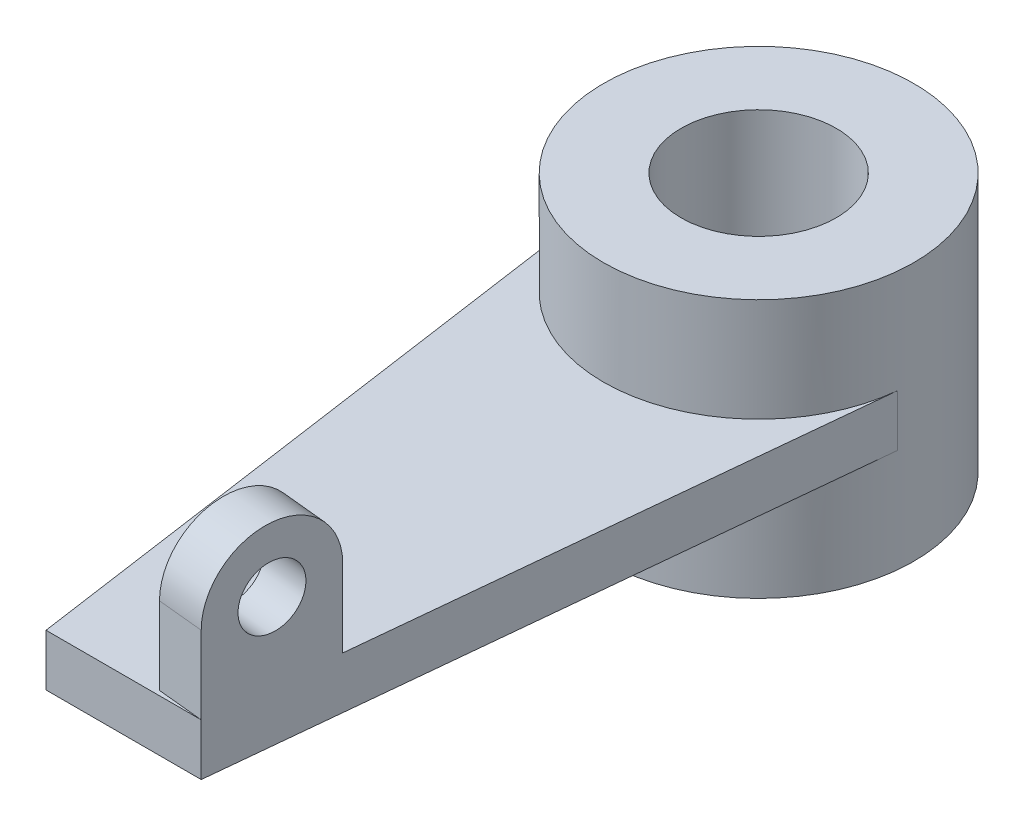
SolidWorks part; units mm, degrees
ref_plane "Front Plane" through (0, 0, 0) normal (0, 0, 1) x (1, 0, 0)
ref_plane "Top Plane" through (0, 0, 0) normal (0, 1, 0) x (1, 0, 0)
ref_plane "Right Plane" through (0, 0, 0) normal (1, 0, 0) x (0, 0, -1)
sketch "Sketch9" plane through (0, 0, 0) normal (0, 1, 0) x (1, 0, 0)
  circle A0 centre (0, 0) radius 30
  circle A1 centre (0, 0) radius 15
  dimension "D1" = 60
  dimension "D2" = 30
extrude "Boss-Extrude4" add sketch "Sketch9" along normal mid plane 50
ref_plane "Plane6" through (0, 0, 0) normal (0, 1, 0) x (1, 0, 0)
sketch "Sketch10" plane through (0, 0, 0) normal (0, 1, 0) x (1, 0, 0)
  line L0 (29.859, -2.9048) -> (17.6552, -125.4048)
  line L1 (17.6552, -125.4048) -> (-12.3448, -125.4048)
  line L2 (-12.3448, -125.4048) -> (-29.859, -2.9048)
  line L3 (29.859, -2.9048) -> (-29.859, -2.9048)
  circle A0 centre (0, 0) radius 30 construction
  point P4 (-128.6774, 25.482)
  dimension "D1" = 122.5
  dimension "D2" = 30
  dimension "D3" = 122.5
extrude "Boss-Extrude5" add sketch "Sketch10" along normal mid plane 10
sketch "Sketch11" plane through (0, 5, 0) normal (0, 1, 0) x (1, 0, 0)
  line L0 (-14.716, -2.9048) -> (14.716, -2.9048)
  arc A0 (14.716, -2.9048) -> (-14.716, -2.9048) centre (0, 0) cw
extrude "Cut-Extrude2" cut sketch "Sketch11" against normal blind 99
sketch "Sketch12" plane through (29.8521, 0, 2.974) normal (0.9951, 0, 0.0991) x (0.0991, 0, -0.9951)
  line L0 (-123.0369, 20) -> (-123.0369, 5)
  line L2 (-98.0369, 20) -> (-98.0369, 5)
  line L3 (-123.0369, 5) -> (-0.0695, 5) construction
  line L4 (-98.0369, 5) -> (-123.0369, 5)
  circle A0 centre (-110.5369, 20) radius 6
  arc A1 (-98.0369, 20) -> (-123.0369, 20) centre (-110.5369, 20) ccw
  point P2 (0, 0)
  point P5 (-110.5369, 5)
  point P12 (0, 0)
  point P13 (0, 0)
  dimension "D1" = 12
  dimension "D2" = 25
  dimension "D3" = 15
extrude "Boss-Extrude6" add sketch "Sketch12" against normal blind 9
sketch "Sketch13" plane through (-29.6679, 0, 4.2417) normal (-0.9899, 0, 0.1415) x (0.1415, 0, 0.9899)
  line L0 (122.3952, 5) -> (97.3952, 5)
  line L1 (1.3505, 5) -> (122.3952, 5) construction
  line L2 (97.3952, 5) -> (97.3952, 20)
  line L3 (122.3952, 5) -> (122.3952, 20)
  line L4 (122.3952, 5) -> (131.3952, 5)
  circle A0 centre (109.8952, 20) radius 6
  arc A1 (122.3952, 20) -> (97.3952, 20) centre (109.8952, 20) ccw
  point P9 (109.8952, 5)
  dimension "D3" = 25
  dimension "D4" = 12
  dimension "D1" = 25
  dimension "D2" = 15
